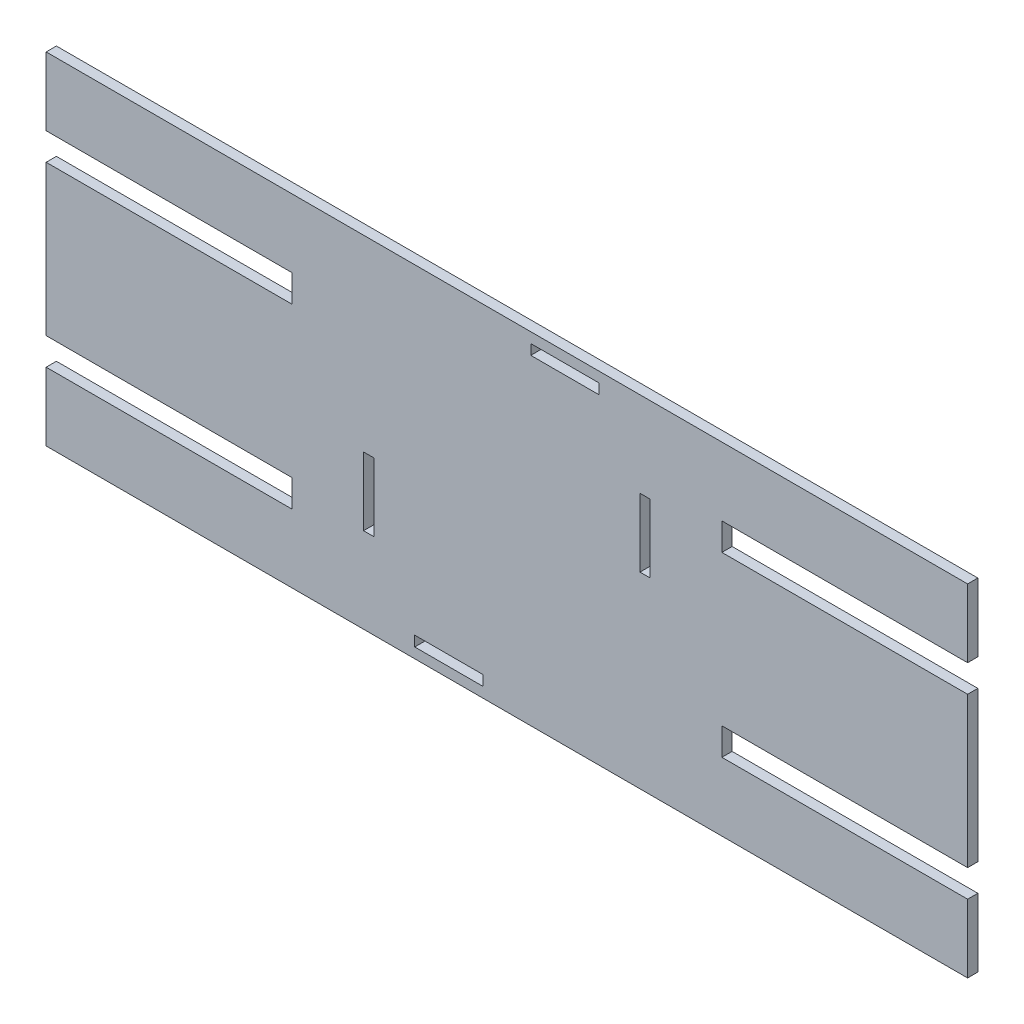
SolidWorks part; units mm, degrees
ref_plane "Спереди" through (0, 0, 0) normal (0, 0, 1) x (1, 0, 0)
ref_plane "Сверху" through (0, 0, 0) normal (0, 1, 0) x (1, 0, 0)
ref_plane "Справа" through (0, 0, 0) normal (1, 0, 0) x (0, 0, -1)
sketch "Эскиз1" plane through (0, 0, 0) normal (0, 0, 1) x (1, 0, 0)
  line L21 (18, 6) -> (38, 6)
  line L22 (0, 0) -> (90, 0)
  line L24 (0, 100) -> (90, 100)
  line L26 (18, 6) -> (18, 3)
  line L27 (18, 3) -> (38, 3)
  line L28 (38, 6) -> (38, 3)
  line L29 (52, 97) -> (72, 97)
  line L30 (52, 97) -> (52, 94)
  line L31 (52, 94) -> (72, 94)
  line L32 (72, 97) -> (72, 94)
  line L33 (0, 100) -> (-90, 100)
  line L34 (3, 45) -> (6, 45)
  line L35 (3, 45) -> (3, 25)
  line L36 (3, 25) -> (6, 25)
  line L37 (6, 45) -> (6, 25)
  line L38 (84, 75) -> (87, 75)
  line L39 (84, 75) -> (84, 55)
  line L40 (84, 55) -> (87, 55)
  line L41 (87, 75) -> (87, 55)
  line L42 (-90, 100) -> (-90, 80)
  line L43 (-90, 0) -> (0, 0)
  line L44 (90, 100) -> (180, 100)
  line L45 (180, 100) -> (180, 80)
  line L46 (180, 0) -> (90, 0)
  line L47 (-1024.1525, 80) -> (45, 80) construction
  line L48 (-1024.1525, 72) -> (-18, 72) construction
  line L49 (-1000, 50) -> (-18, 50) construction
  line L50 (-18, -913.4928) -> (-18, 49086.5072) construction
  line L51 (-90, 80) -> (-18, 80)
  line L52 (-18, 80) -> (-18, 72)
  line L53 (-18, 72) -> (-90, 72)
  line L54 (-90, 72) -> (-90, 28)
  line L55 (-18, 20) -> (-18, 28)
  line L56 (-18, 28) -> (-90, 28)
  line L57 (-90, 20) -> (-18, 20)
  line L58 (45, -1000) -> (45, 49000) construction
  line L59 (108, 20) -> (108, 28)
  line L60 (180, 20) -> (108, 20)
  line L61 (108, 28) -> (180, 28)
  line L62 (108, 80) -> (108, 72)
  line L63 (108, 72) -> (180, 72)
  line L64 (180, 80) -> (108, 80)
  line L65 (-90, 20) -> (-90, 0)
  line L66 (180, 20) -> (180, 0)
  line L67 (180, 72) -> (180, 28)
  line L68 (-24.1525, 72) -> (45, 72) construction
  line L69 (0, 50) -> (90, 50) construction
  line L70 (180, 50) -> (49000, 50) construction
  line L71 (65.8475, 72) -> (48975.8475, 72) construction
  line L72 (108, 80) -> (48975.8475, 80) construction
  line L73 (0, -884.0101) -> (0, 49115.9899) construction
  line L74 (90, -900) -> (90, 49100) construction
  point P45 (45, 0)
  dimension "D1" = 3
  dimension "D2" = 20
  dimension "D3" = 3
  dimension "D4" = 20
  dimension "D5" = 100
  dimension "D6" = 90
  dimension "D7" = 72
  dimension "D8" = 90
  dimension "D9" = 3
  dimension "D10" = 3
  dimension "D11" = 20
  dimension "D12" = 20
  dimension "D13" = 3
  dimension "D14" = 3
  dimension "D15" = 78
  dimension "D16" = 7
  dimension "D17" = 25
  dimension "D18" = 25
  dimension "D19" = 18
  dimension "D20" = 90
  dimension "D21" = 8
  dimension "D22" = 20
  dimension "D23" = 270
  dimension "D24" = 3
extrude "Бобышка-Вытянуть1" add sketch "Эскиз1" along normal blind 3
